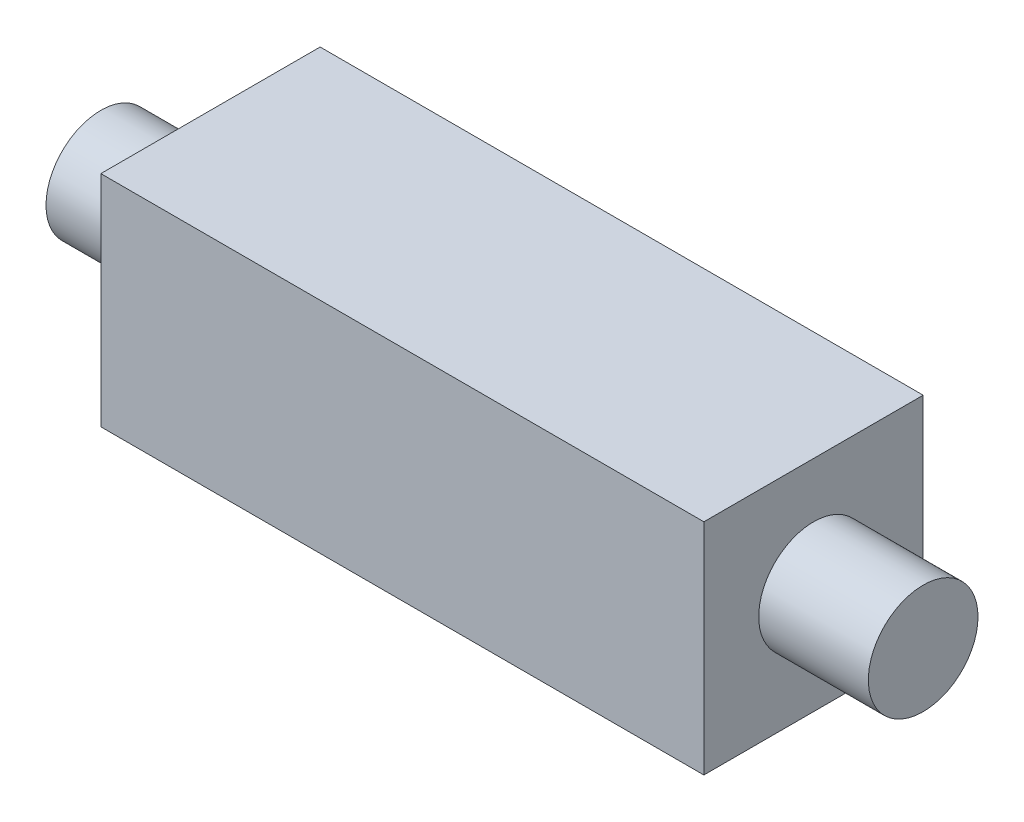
SolidWorks part; units mm, degrees
ref_plane "Front Plane" through (0, 0, 0) normal (0, 0, 1) x (1, 0, 0)
ref_plane "Top Plane" through (0, 0, 0) normal (0, 1, 0) x (1, 0, 0)
ref_plane "Right Plane" through (0, 0, 0) normal (1, 0, 0) x (0, 0, -1)
sketch "Sketch1" plane through (0, 0, 0) normal (0, 1, 0) x (1, 0, 0)
  line L1 (-5.5, 2) -> (5.5, 2)
  line L2 (-5.5, 2) -> (-5.5, -2)
  line L3 (-5.5, -2) -> (5.5, -2)
  line L4 (5.5, 2) -> (5.5, -2)
  line L5 (-5.5, 2) -> (5.5, -2) construction
  line L6 (-5.5, -2) -> (5.5, 2) construction
  point P0 (0, 0)
extrude "Boss-Extrude1" add sketch "Sketch1" along normal blind 4
sketch "Sketch2" plane through (5.5, 0, 0) normal (1, 0, 0) x (0, 0, -1)
  circle A0 centre (0, 2) radius 1
extrude "Boss-Extrude2" add sketch "Sketch2" along normal blind 2
sketch "Sketch3" plane through (-5.5, 0, 0) normal (-1, 0, 0) x (0, 0, 1)
  circle A0 centre (0, 2) radius 1
extrude "Boss-Extrude3" add sketch "Sketch3" along normal blind 2
